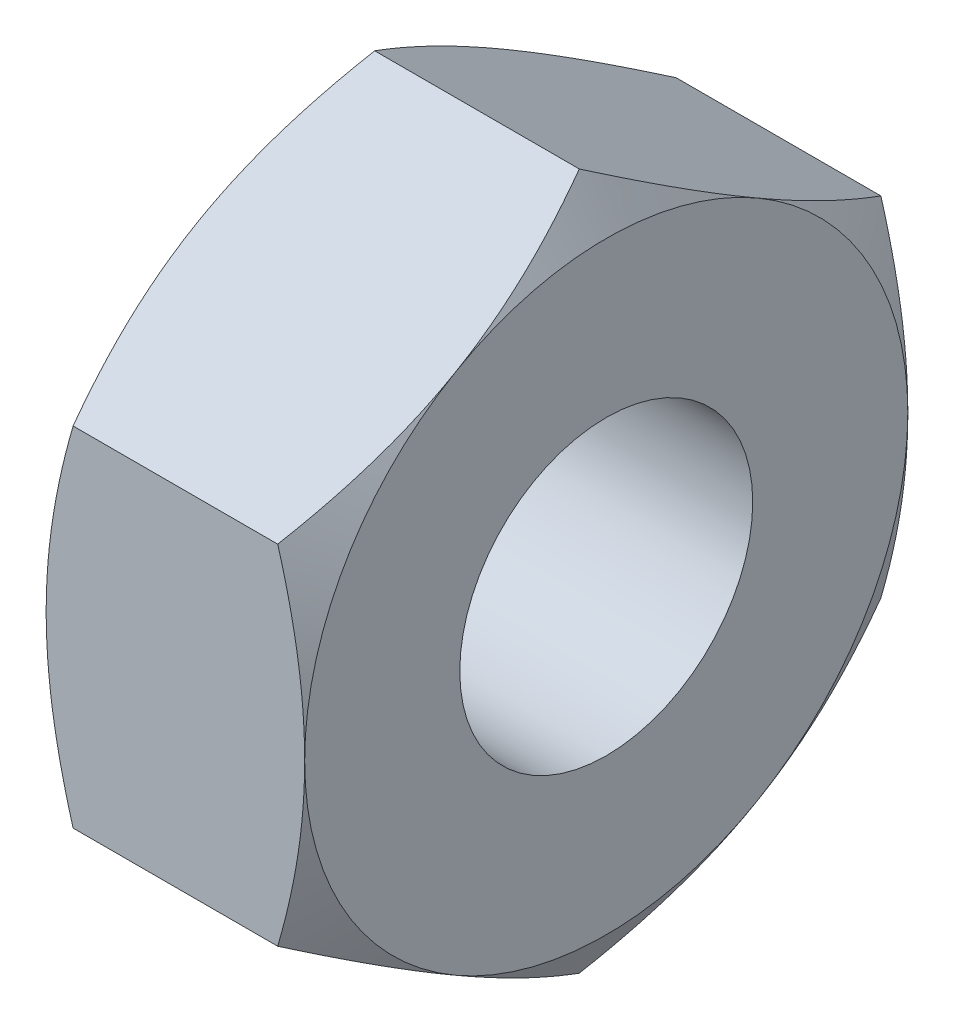
SolidWorks part; units mm, degrees
ref_plane "Plan1" through (0, 0, 0) normal (0, 0, 1) x (1, 0, 0)
ref_plane "Plan2" through (0, 0, 0) normal (0, 1, 0) x (1, 0, 0)
ref_plane "Plan3" through (0, 0, 0) normal (1, 0, 0) x (0, 0, -1)
sketch "Esquisse1" plane through (0, 0, 0) normal (0, 0, 1) x (1, 0, 0)
  line L0 (-3, 0) -> (3, 0)
  line L1 (-3, 0) -> (-3, 7)
  line L2 (3, 0) -> (3, 7)
  line L3 (-3, 7) -> (0, 12.1962)
  line L4 (3, 7) -> (0, 12.1962)
  line L6 (-10.7556, 0) -> (10.7556, 0) construction
  dimension "D1" = 60
  dimension "D3" = 7
  dimension "D4" = 6
revolve "Base-Révolution" add sketch "Esquisse1" angle 360 about L6
sketch "Esquisse2" plane through (-3, 0, 0) normal (-1, 0, 0) x (0, 0, 1)
  line L0 (0, 8.0829) -> (0, -8.0829) construction
  line L1 (0, 8.0829) -> (7, 4.0415)
  line L2 (7, 4.0415) -> (7, -4.0415)
  line L3 (7, -4.0415) -> (0, -8.0829)
  line L4 (-7, -4.0415) -> (0, -8.0829)
  line L5 (-7, 4.0415) -> (-7, -4.0415)
  line L6 (0, 8.0829) -> (-7, 4.0415)
  line L7 (0, 19.6299) -> (17, 9.815)
  line L8 (17, 9.815) -> (17, -9.815)
  line L9 (17, -9.815) -> (0, -19.6299)
  line L10 (-17, -9.815) -> (0, -19.6299)
  line L11 (-17, 9.815) -> (-17, -9.815)
  line L12 (0, 19.6299) -> (-17, 9.815)
  circle A0 centre (0, 0) radius 7 construction
  dimension "D3" = 10
  dimension "D1" = 120
extrude "Enlèv. mat.-Extru.1" cut sketch "Esquisse2" against normal through all
hole_wizard "Perçage2" positions "Esquisse6" profile "Esquisse5" tap size "M8x1.25" standard "ISO"
sketch "Esquisse6" plane through (3, 0, 0) normal (1, 0, 0) x (0, 0, -1)
  point P0 (0, 0)
sketch "Esquisse5" plane through (3, 0, 0) normal (0, 1, 0) x (0, 0, -1)
  line L0 (0, 0) -> (0, 24.2929)
  line L1 (0, 24.2929) -> (3.4, 22.25)
  line L2 (3.4, 22.25) -> (3.4, 0)
  line L5 (3.4, 0) -> (0, 0)
  line L10 (0, 24.2929) -> (-3.4, 22.25) construction
  line L11 (0, -6.35) -> (0, 107.95) construction
  dimension "Diamètre du perçage" = 6.8
  dimension "Profondeur du perçage" = 22.25
  dimension "Angle de pointe" = 118
cosmetic thread "Représentation de filetage3" parameters "D1"=6, "D2"=8
